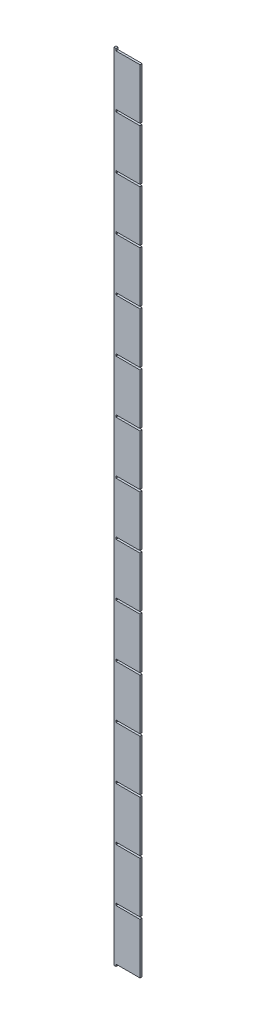
SolidWorks part; units mm, degrees
material "Cedar"
ref_plane "Front Plane" through (0, 0, 0) normal (0, 0, 1) x (1, 0, 0)
ref_plane "Top Plane" through (0, 0, 0) normal (0, 1, 0) x (1, 0, 0)
ref_plane "Right Plane" through (0, 0, 0) normal (1, 0, 0) x (0, 0, -1)
sketch "Sketch1" plane through (0, 0, 0) normal (0, 0, 1) x (1, 0, 0)
  line L0 (-9.0825, 748) -> (-9.0825, 752)
  line L1 (-9.0825, 752) -> (-13.0825, 752)
  line L2 (-13.0825, 752) -> (-13.0825, -752)
  line L3 (-9.0825, 748) -> (36.3023, 748)
  line L4 (36.3023, 748) -> (36.3023, 652)
  line L5 (36.3023, 652) -> (-9.081, 652)
  line L6 (-5.8202, -752) -> (-36.3023, -752) construction
  line L7 (-13.0825, -752) -> (-9.0825, -752)
  line L8 (-9.0825, 648) -> (36.3023, 648)
  line L9 (36.3023, 648) -> (36.3023, 552)
  line L10 (-9.081, 652) -> (-9.0825, 648)
  line L11 (36.3023, 552) -> (-9.081, 552)
  line L12 (-9.081, 552) -> (-9.0825, 548)
  line L13 (-9.0825, 548) -> (36.3023, 548)
  line L14 (36.3023, 548) -> (36.3023, 452)
  line L15 (36.3023, 452) -> (-9.081, 452)
  line L16 (-9.081, 452) -> (-9.0825, 448)
  line L17 (-9.0825, 448) -> (36.3023, 448)
  line L18 (36.3023, 448) -> (36.3023, 352)
  line L19 (36.3023, 352) -> (-9.081, 352)
  line L20 (-9.081, 352) -> (-9.0825, 348)
  line L21 (-9.0825, 348) -> (36.3023, 348)
  line L22 (36.3023, 348) -> (36.3023, 252)
  line L23 (36.3023, 252) -> (-9.081, 252)
  line L24 (-9.081, 252) -> (-9.0825, 248)
  line L25 (-9.0825, 248) -> (36.3023, 248)
  line L26 (36.3023, 248) -> (36.3023, 152)
  line L27 (36.3023, 152) -> (-9.081, 152)
  line L28 (-9.081, 152) -> (-9.0825, 148)
  line L29 (-9.0825, 148) -> (36.3023, 148)
  line L30 (36.3023, 148) -> (36.3023, 52)
  line L31 (36.3023, 52) -> (-9.081, 52)
  line L32 (-9.081, 52) -> (-9.0825, 48)
  line L33 (-9.0825, 48) -> (36.3023, 48)
  line L34 (36.3023, 48) -> (36.3023, -48)
  line L35 (36.3023, -48) -> (-9.081, -48)
  line L36 (-9.081, -48) -> (-9.0825, -52)
  line L37 (-9.0825, -52) -> (36.3023, -52)
  line L38 (36.3023, -52) -> (36.3023, -148)
  line L39 (36.3023, -148) -> (-9.081, -148)
  line L40 (-9.081, -148) -> (-9.0825, -152)
  line L41 (-9.0825, -152) -> (36.3023, -152)
  line L42 (36.3023, -152) -> (36.3023, -248)
  line L43 (36.3023, -248) -> (-9.081, -248)
  line L44 (-9.081, -248) -> (-9.0825, -252)
  line L45 (-9.0825, -252) -> (36.3023, -252)
  line L46 (36.3023, -252) -> (36.3023, -348)
  line L47 (36.3023, -348) -> (-9.081, -348)
  line L48 (-9.081, -348) -> (-9.0825, -352)
  line L49 (-9.0825, -352) -> (36.3023, -352)
  line L50 (36.3023, -352) -> (36.3023, -448)
  line L51 (36.3023, -448) -> (-9.081, -448)
  line L52 (-9.081, -448) -> (-9.0825, -452)
  line L53 (-9.0825, -452) -> (36.3023, -452)
  line L54 (36.3023, -452) -> (36.3023, -548)
  line L55 (36.3023, -548) -> (-9.081, -548)
  line L56 (-9.081, -548) -> (-9.0825, -552)
  line L57 (-9.0825, -552) -> (36.3023, -552)
  line L58 (36.3023, -552) -> (36.3023, -648)
  line L59 (36.3023, -648) -> (-9.081, -648)
  line L60 (-9.081, -648) -> (-9.0825, -652)
  line L61 (-9.0825, -652) -> (36.3023, -652)
  line L62 (36.3023, -652) -> (36.3023, -748)
  line L63 (36.3023, -748) -> (-9.081, -748)
  line L64 (-9.081, -748) -> (-9.0825, -752)
  dimension "D1" = 4
  dimension "D2" = 45.3847
  dimension "D3" = 15
extrude "Boss-Extrude1" add sketch "Sketch1" along normal blind 4
